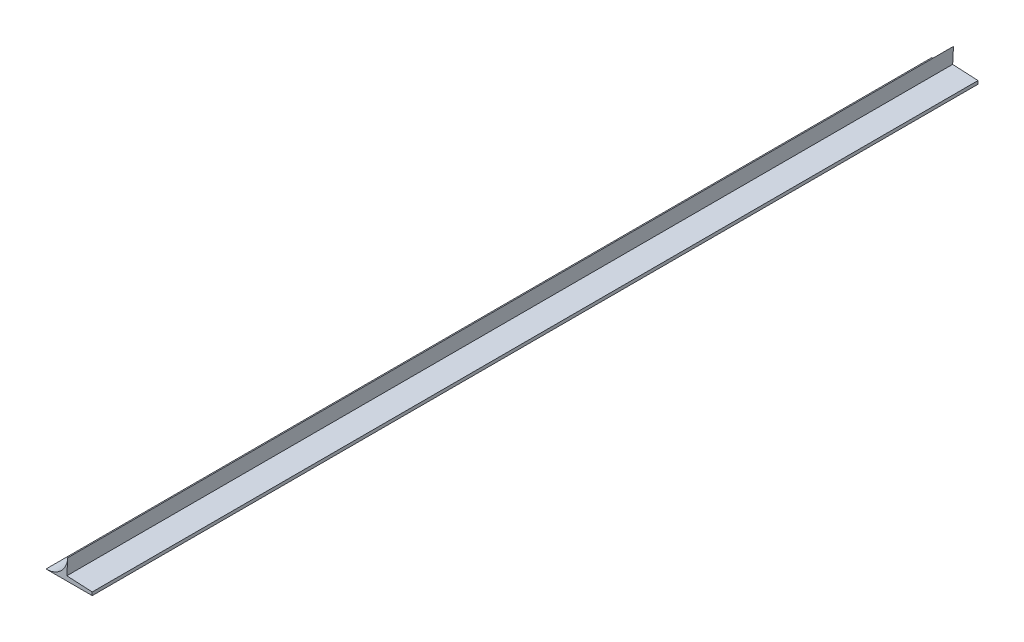
SolidWorks part; units mm, degrees
ref_plane "Front Plane" through (0, 0, 0) normal (0, 0, 1) x (1, 0, 0)
ref_plane "Top Plane" through (0, 0, 0) normal (0, 1, 0) x (1, 0, 0)
ref_plane "Right Plane" through (0, 0, 0) normal (1, 0, 0) x (0, 0, -1)
sketch "Sketch1" plane through (0, 0, 0) normal (0, 0, 1) x (1, 0, 0)
  line L0 (0, 0) -> (13.48, 0)
  line L1 (13.48, 2.7974) -> (13.48, 12.79) construction
  line L3 (28.695, 0) -> (13.48, 0)
  line L4 (13.48, 12.79) -> (12.9577, 2.8248)
  line L5 (13.48, 2.7974) -> (12.9577, 2.8248)
  line L6 (13.48, 2.7974) -> (28.695, 2)
  line L8 (28.695, 2) -> (28.695, 0)
  arc A0 (13.48, 12.79) -> (0, 0) centre (-0.0013, 13.5) cw
  dimension "D1" = 13.48
  dimension "D3" = 93
  dimension "D4" = 15.47
  dimension "D2" = 13.5
  dimension "D5" = 12.79
  dimension "D6" = 2
extrude "Boss-Extrude1" add sketch "Sketch1" along normal blind 550 contours A0 L0 L3 L8 L6 L5 L4
